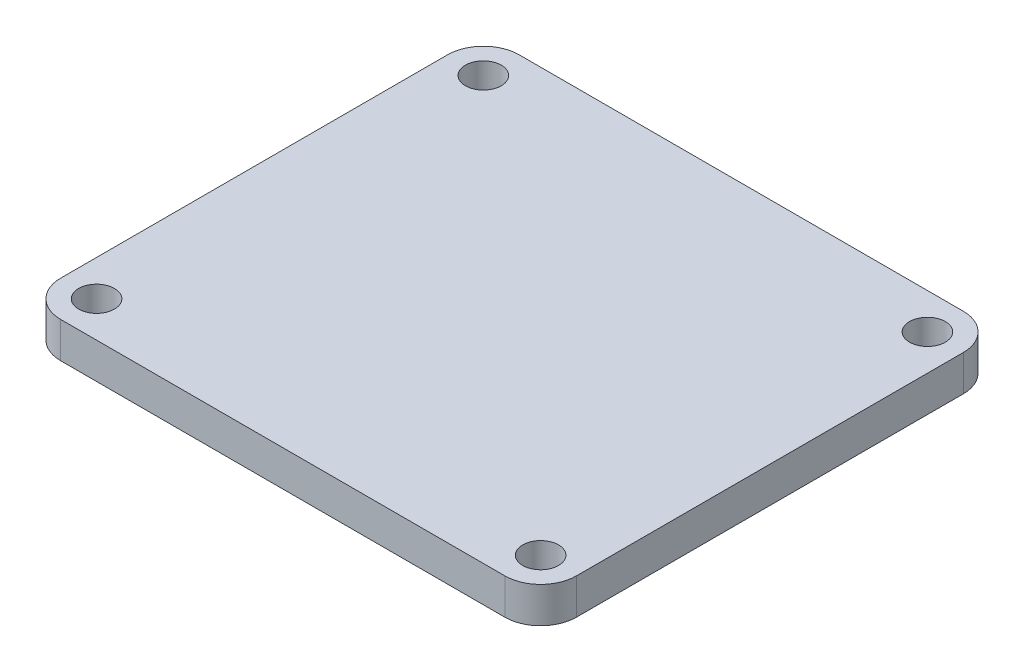
SolidWorks part; units mm, degrees
ref_plane "Front Plane" through (0, 0, 0) normal (0, 0, 1) x (1, 0, 0)
ref_plane "Top Plane" through (0, 0, 0) normal (0, 1, 0) x (1, 0, 0)
ref_plane "Right Plane" through (0, 0, 0) normal (1, 0, 0) x (0, 0, -1)
sketch "Sketch1" plane through (0, 0, 0) normal (0, 1, 0) x (1, 0, 0)
  line L0 (3.9158, 17.5579) -> (3.9158, -46.4421)
  line L1 (-32.0842, 17.5579) -> (39.9158, 17.5579)
  line L2 (-32.0842, 17.5579) -> (-32.0842, -46.4421)
  line L3 (-32.0842, -46.4421) -> (39.9158, -46.4421)
  line L4 (39.9158, 17.5579) -> (39.9158, -46.4421)
  circle A0 centre (34.9158, 12.5579) radius 2.5
  circle A1 centre (-27.0842, 12.5579) radius 2.5
  circle A2 centre (34.9158, -41.4421) radius 2.5
  circle A3 centre (-27.0842, -41.4421) radius 2.5
  dimension "D3" = 5
  dimension "D1" = 72
  dimension "D2" = 64
  dimension "D4" = 5
  dimension "D5" = 5
  dimension "D6" = 5
extrude "Boss-Extrude1" add sketch "Sketch1" along normal blind 5
fillet "Fillet1" radius 5 4 edges at (-32.0842, 2.5, 46.4421) (39.9158, 2.5, 46.4421) (39.9158, 2.5, -17.5579) (-32.0842, 2.5, -17.5579)
